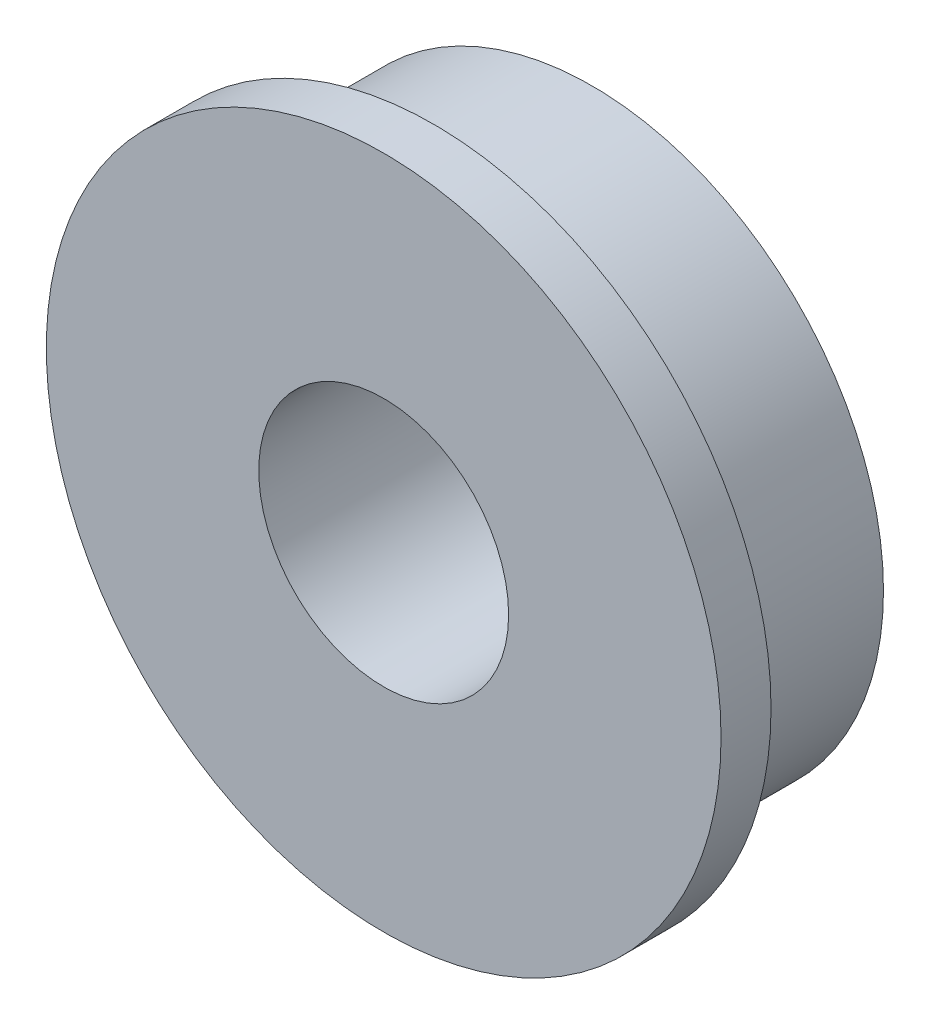
SolidWorks part; units mm, degrees
material "合金钢"
ref_plane "前视基准面" through (0, 0, 0) normal (0, 0, 1) x (1, 0, 0)
ref_plane "上视基准面" through (0, 0, 0) normal (0, 1, 0) x (1, 0, 0)
ref_plane "右视基准面" through (0, 0, 0) normal (1, 0, 0) x (0, 0, -1)
sketch "草图1" plane through (0, 0, 0) normal (0, 0, 1) x (1, 0, 0)
  circle A0 centre (0, 0) radius 1.5
  circle A1 centre (0, 0) radius 3.5
  dimension "D1" = 3
  dimension "D2" = 7
extrude "凸台-拉伸1" add sketch "草图1" along normal blind 2.5
sketch "草图2" plane through (0, 0, 2.5) normal (0, 0, 1) x (1, 0, 0)
  circle A0 centre (0, 0) radius 1.5
  circle A1 centre (0, 0) radius 4.05
  circle A2 centre (0, 0) radius 1.5 construction
  dimension "D1" = 8.1
extrude "凸台-拉伸2" add sketch "草图2" against normal blind 0.6
